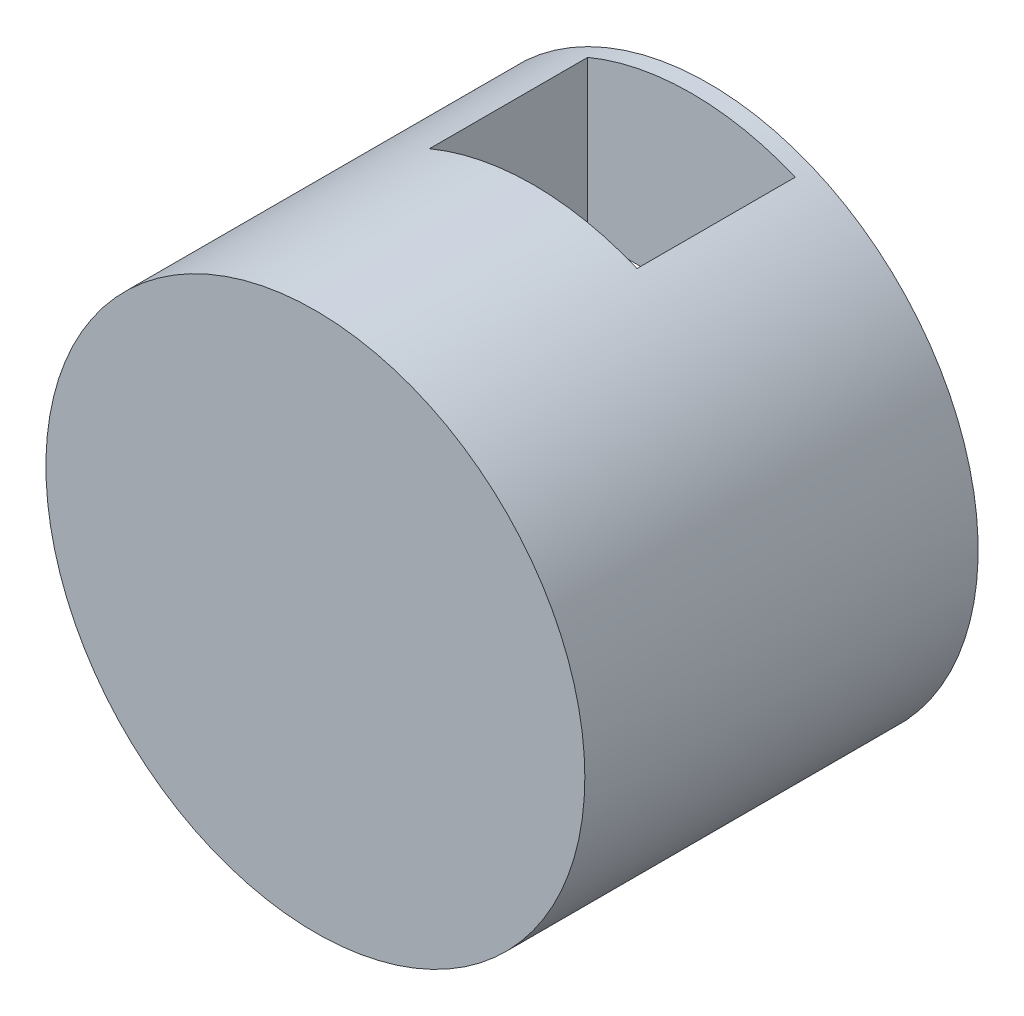
SolidWorks part; units mm, degrees
ref_plane "Front Plane" through (0, 0, 0) normal (0, 0, 1) x (1, 0, 0)
ref_plane "Top Plane" through (0, 0, 0) normal (0, 1, 0) x (1, 0, 0)
ref_plane "Right Plane" through (0, 0, 0) normal (1, 0, 0) x (0, 0, -1)
sketch "Sketch1" plane through (0, 0, 0) normal (0, 0, 1) x (1, 0, 0)
  circle A0 centre (0, 0) radius 23.5
  dimension "D1" = 47
extrude "Boss-Extrude1" add sketch "Sketch1" along normal blind 32.8 contours A0
sketch "Sketch5" plane through (0, 0, 0) normal (0, 0, -1) x (-1, 0, 0)
  line L1 (-9.05, 23.5) -> (9.05, 23.5)
  line L2 (-9.05, 23.5) -> (-9.05, -23.5)
  line L3 (-9.05, -23.5) -> (9.05, -23.5)
  line L4 (9.05, 23.5) -> (9.05, -23.5)
  dimension "D1" = 47
  dimension "D2" = 23.5
  dimension "D3" = 18.1
  dimension "D4" = 9.05
extrude "Cut-Extrude1" cut sketch "Sketch5" against normal blind 13.8
sketch "Sketch6" plane through (0, 0, 0) normal (0, 0, 1) x (1, 0, 0)
  circle A0 centre (0, 0) radius 23.5
  dimension "D1" = 47
extrude "Boss-Extrude2" add sketch "Sketch6" against normal blind 1.5
sketch "Sketch8" plane through (0, 0, -1.5) normal (0, 0, -1) x (-1, 0, 0)
  line L0 (-9.05, 8.2) -> (9.05, 8.2)
  line L2 (9.05, -21.6875) -> (9.05, 21.6875)
  line L3 (-9.05, 21.6875) -> (-9.05, -21.6875)
  line L4 (9.05, -21.6875) -> (9.05, 8.2)
  line L5 (-9.05, 8.2) -> (-9.05, -21.6875)
  arc A2 (9.05, 21.6875) -> (-9.05, 21.6875) centre (0, 0) ccw
  arc A3 (-9.05, -21.6875) -> (9.05, -21.6875) centre (0, 0) ccw
  arc A5 (-9.05, -21.6875) -> (9.05, -21.6875) centre (0, 0) ccw
  dimension "D2" = 8.2
  dimension "D1" = 0
extrude "Cut-Extrude5" cut sketch "Sketch8" against normal blind 1.5
